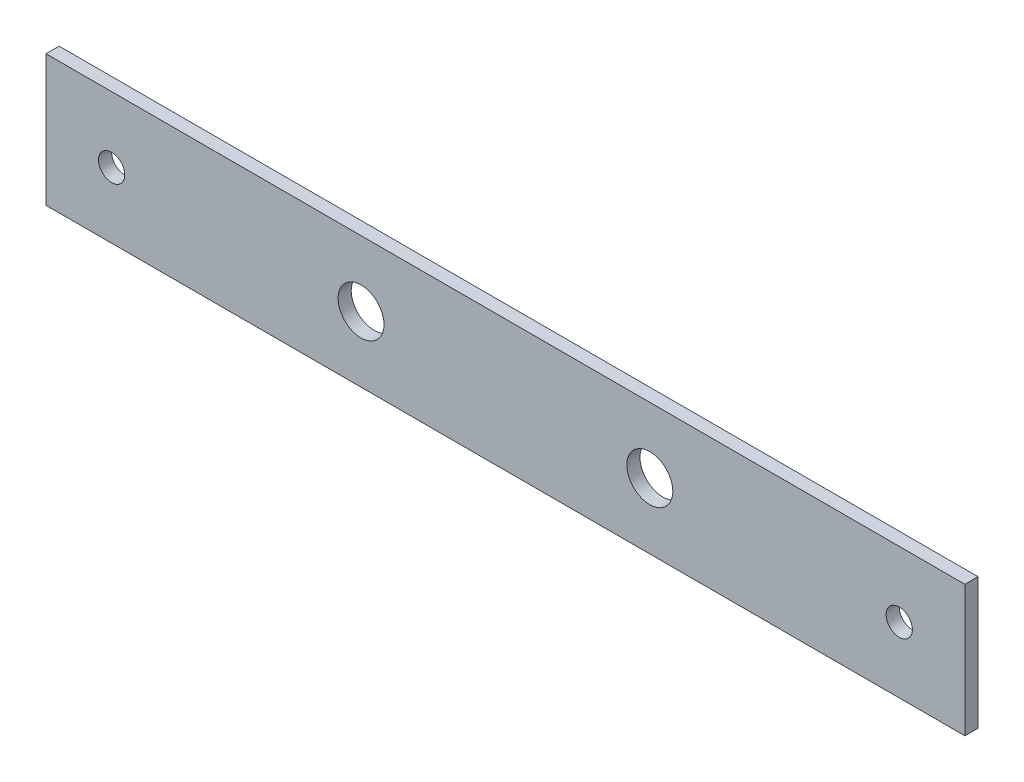
SolidWorks part; units mm, degrees
material "7075-T6 (SN)"
ref_plane "Front Plane" through (0, 0, 0) normal (0, 0, 1) x (1, 0, 0)
ref_plane "Top Plane" through (0, 0, 0) normal (0, 1, 0) x (1, 0, 0)
ref_plane "Right Plane" through (0, 0, 0) normal (1, 0, 0) x (0, 0, -1)
sketch "Sketch1" plane through (0, 0, 0) normal (0, 0, 1) x (1, 0, 0)
  line L1 (-70, -10) -> (70, -10)
  line L2 (-70, -10) -> (-70, 10)
  line L3 (-70, 10) -> (70, 10)
  line L4 (70, -10) -> (70, 10)
  line L5 (-70, -10) -> (70, 10) construction
  line L6 (-70, 10) -> (70, -10) construction
  point P0 (0, 0)
  dimension "D1" = 20
  dimension "D2" = 140
extrude "Boss-Extrude1" add sketch "Sketch1" along normal blind 2
sketch "Sketch2" plane through (0, 0, 2) normal (0, 0, 1) x (1, 0, 0)
  line L0 (-77.6256, 0) -> (87.5667, 0) construction
  line L1 (60, 15.7225) -> (60, -15.6799) construction
  line L2 (-60, 19.153) -> (-60, -16.7355) construction
  line L3 (-70, 10) -> (-70, -10) construction
  line L4 (70, -10) -> (70, 10) construction
  circle A0 centre (-60, 0) radius 2
  circle A1 centre (60, 0) radius 2
  dimension "D3" = 4
  dimension "D4" = 4
  dimension "D1" = 10
  dimension "D2" = 10
extrude "Cut-Extrude1" cut sketch "Sketch2" against normal through all
sketch "Sketch3" plane through (0, 0, 2) normal (0, 0, 1) x (1, 0, 0)
  line L0 (0, 35.736) -> (0, -36.0203) construction
  line L1 (-22, 0) -> (22, 0) construction
  circle A0 centre (22, 0) radius 3.5
  circle A1 centre (-22, 0) radius 3.5
  point P5 (0, 0)
  dimension "D2" = 7
  dimension "D3" = 7
  dimension "D1" = 44
extrude "Cut-Extrude2" cut sketch "Sketch3" against normal up to next
